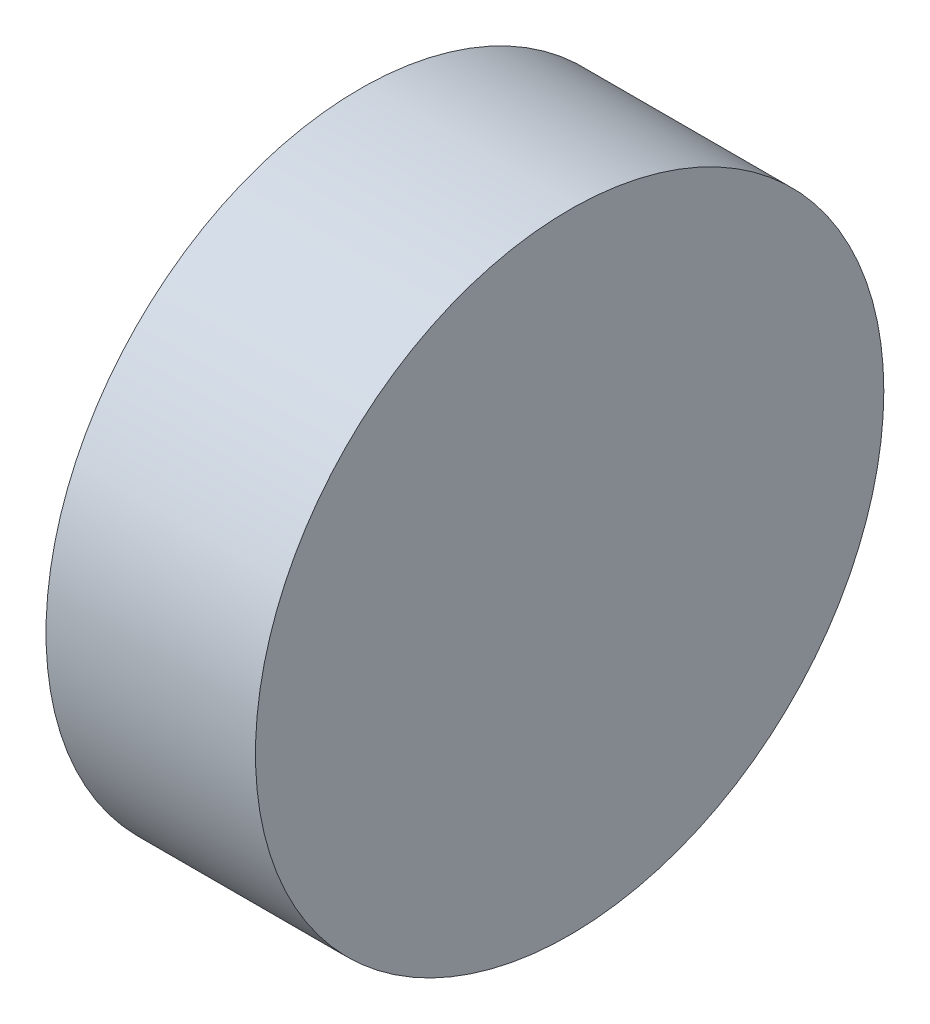
SolidWorks part; units mm, degrees
ref_plane "Front Plane" through (0, 0, 0) normal (0, 0, 1) x (1, 0, 0)
ref_plane "Top Plane" through (0, 0, 0) normal (0, 1, 0) x (1, 0, 0)
ref_plane "Right Plane" through (0, 0, 0) normal (1, 0, 0) x (0, 0, -1)
sketch "Sketch1" plane through (0, 0, 0) normal (1, 0, 0) x (0, 0, -1)
  circle A0 centre (0, 0) radius 76.2
  dimension "D1" = 152.4
extrude "Boss-Extrude1" add sketch "Sketch1" along normal blind 50.8
